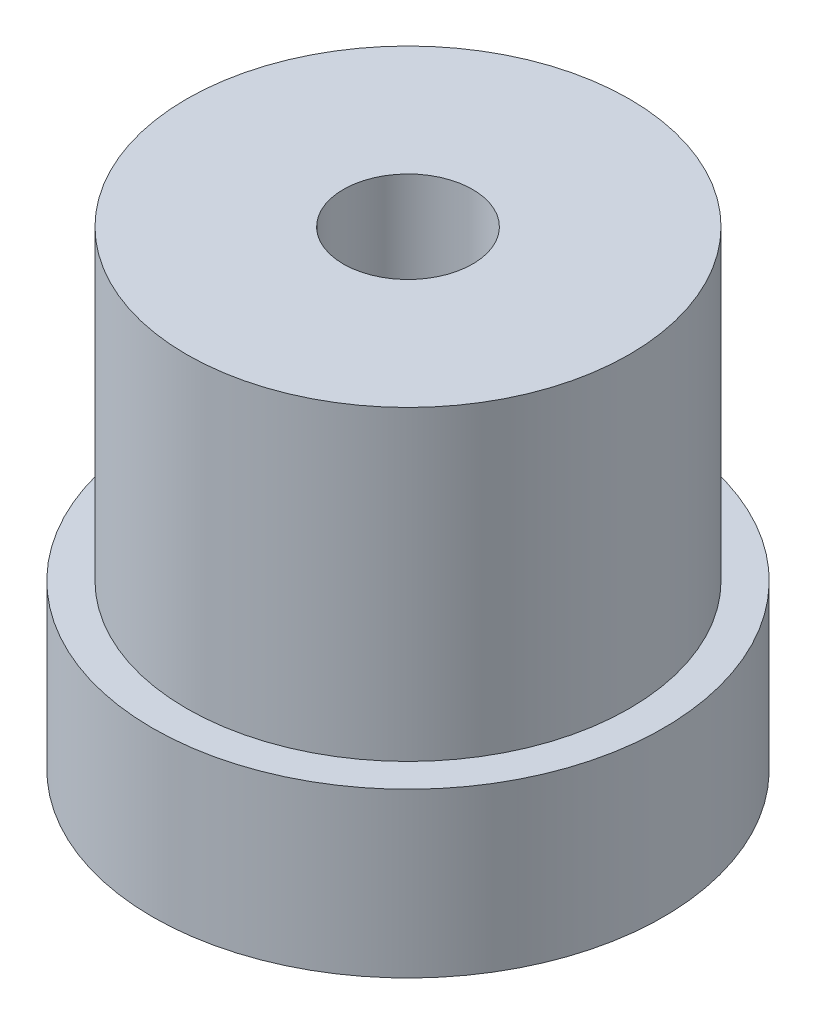
SolidWorks part; units mm, degrees
material "6061-T6 (SS)"
ref_plane "Front Plane" through (0, 0, 0) normal (0, 0, 1) x (1, 0, 0)
ref_plane "Top Plane" through (0, 0, 0) normal (0, 1, 0) x (1, 0, 0)
ref_plane "Right Plane" through (0, 0, 0) normal (1, 0, 0) x (0, 0, -1)
sketch "Sketch1" plane through (0, 0, 0) normal (0, 0, 1) x (1, 0, 0)
  line L0 (0, 0) -> (0, 13.8025) construction
  line L1 (0, 13.8025) -> (6.5, 13.8025)
  line L2 (6.5, 13.8025) -> (6.5, 4.8)
  line L5 (7.5, 0) -> (0, 0)
  line L6 (0, 0) -> (0, 13.8025)
  line L7 (6.5, 4.8) -> (7.5, 4.8)
  line L8 (7.5, 4.8) -> (7.5, 0)
  dimension "D1" = 13.8025
  dimension "D2" = 6.5
  dimension "D3" = 4.8
  dimension "D5" = 1
revolve "Revolve1" add sketch "Sketch1" angle 360 about L0
hole_wizard "M3x0.5 Tapped Hole1" positions "Sketch3" profile "Sketch4" tap size "M3x0.5" standard "ANSI Metric"
sketch "Sketch3" plane through (0, 0, 0) normal (0, -1, 0) x (-1, 0, 0)
  point P0 (0, 5)
  point P35 (4.3301, -2.5)
  point P36 (-4.3301, -2.5)
  dimension "D1" = 5
  dimension "D2" = 3
cosmetic thread "Hole Thread4"
cosmetic thread "Hole Thread5"
cosmetic thread "Hole Thread6"
sketch "Sketch4" plane through (0, 0, -5) normal (1, 0, 0) x (0, 0, -1)
  line L0 (0, 0) -> (0, 8.2511)
  line L1 (0, 8.2511) -> (1.25, 7.5)
  line L2 (1.25, 7.5) -> (1.25, 0)
  line L5 (1.25, 0) -> (0, 0)
  line L10 (0, 8.2511) -> (-1.25, 7.5) construction
  line L11 (0, -6.35) -> (0, 107.95) construction
  dimension "Tap Drill Dia." = 2.5
  dimension "Tap Drill Depth" = 7.5
  dimension "Drill Angle" = 118
hole_wizard "#10-24 Tapped Hole1" positions "Sketch9" profile "Sketch8" tap size "#10-24" standard "ANSI Inch"
sketch "Sketch9" plane through (0, 13.8025, 0) normal (0, 1, 0) x (1, 0, 0)
  point P0 (0, 0)
sketch "Sketch8" plane through (0, 13.8025, 0) normal (1, 0, 0) x (0, 0, 1)
  line L0 (0, 0) -> (0, 11.1408)
  line L1 (0, 11.1408) -> (1.8986, 10)
  line L2 (1.8986, 10) -> (1.8986, 0)
  line L5 (1.8986, 0) -> (0, 0)
  line L10 (0, 11.1408) -> (-1.8987, 10) construction
  line L11 (0, -6.35) -> (0, 107.95) construction
  dimension "Tap Drill Dia." = 3.7973
  dimension "Tap Drill Depth" = 10
  dimension "Drill Angle" = 118
cosmetic thread "Hole Thread8"
sketch "Sketch10" [suppressed] plane through (0, 4.8, 0) normal (0, 1, 0) x (1, 0, 0)
  circle A0 centre (0, 0) radius 7.5
extrude "Boss-Extrude1" [suppressed] add sketch "Sketch10" along normal up to surface (9.0025 mm away)
